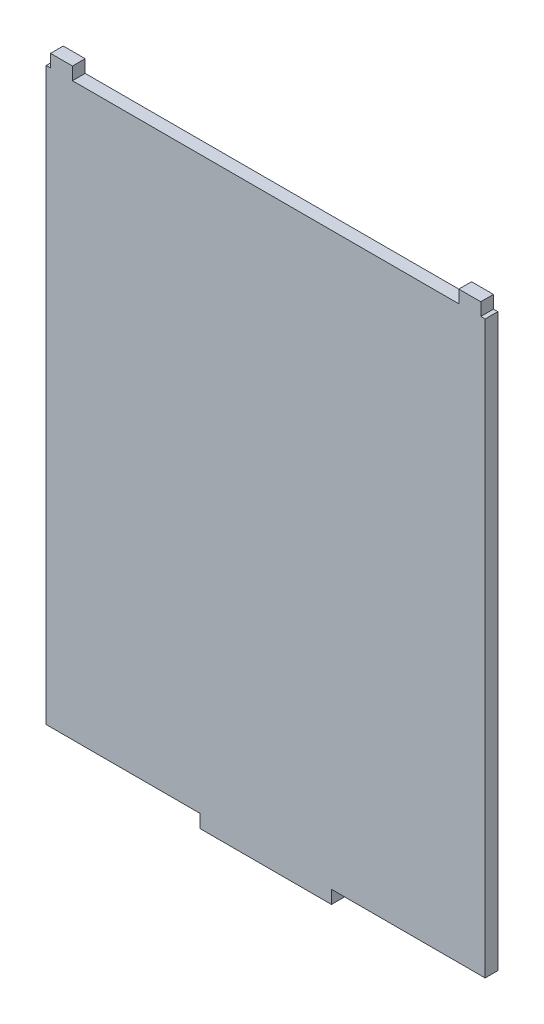
SolidWorks part; units mm, degrees
ref_plane "前视基准面" through (0, 0, 0) normal (0, 0, 1) x (1, 0, 0)
ref_plane "上视基准面" through (0, 0, 0) normal (0, 1, 0) x (1, 0, 0)
ref_plane "右视基准面" through (0, 0, 0) normal (1, 0, 0) x (0, 0, -1)
sketch "草图1" plane through (0, 0, 0) normal (0, 0, 1) x (1, 0, 0)
  line L0 (65, 0) -> (100, 0)
  line L1 (0, 0) -> (35, 0)
  line L2 (0, 0) -> (0, 130)
  line L3 (6, 130) -> (94, 130)
  line L4 (100, 0) -> (100, 130)
  line L7 (50, -3) -> (65, -3)
  line L8 (65, 0) -> (65, -3)
  line L11 (50, -3) -> (35, -3)
  line L12 (35, 0) -> (35, -3)
  line L15 (1, 132.9) -> (5, 132.9)
  line L19 (99, 132.9) -> (95, 132.9)
  line L22 (100, 130) -> (99, 130)
  line L25 (99, 130) -> (99, 132.9)
  line L28 (95, 132.9) -> (94, 132.9)
  line L29 (94, 130) -> (94, 132.9)
  line L30 (0, 130) -> (1, 130)
  line L33 (1, 130) -> (1, 132.9)
  line L36 (5, 132.9) -> (6, 132.9)
  line L37 (6, 130) -> (6, 132.9)
extrude "凸台-拉伸1" add sketch "草图1" along normal blind 2.9
